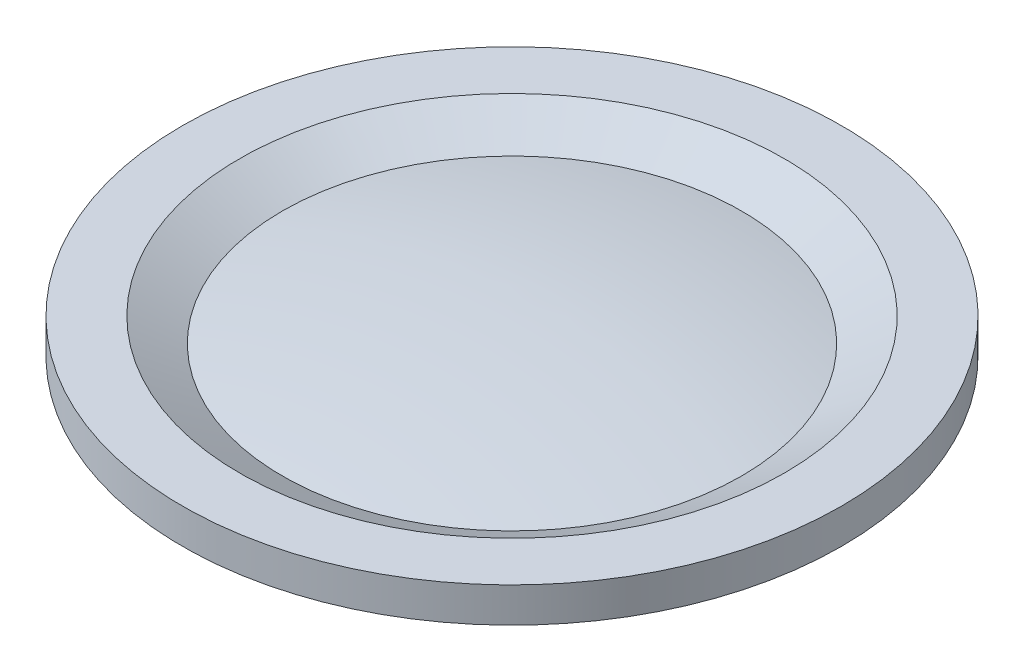
SolidWorks part; units mm, degrees
ref_plane "Front Plane" through (0, 0, 0) normal (0, 0, 1) x (1, 0, 0)
ref_plane "Top Plane" through (0, 0, 0) normal (0, 1, 0) x (1, 0, 0)
ref_plane "Right Plane" through (0, 0, 0) normal (1, 0, 0) x (0, 0, -1)
sketch "Sketch1" plane through (0, 0, 0) normal (0, 0, 1) x (1, 0, 0)
  line L0 (0, 0) -> (-8.1, 0)
  line L1 (-8.1, 0) -> (-8.1, 1.6)
  line L2 (-8.1, 1.6) -> (-14.4, 1.6)
  line L3 (-14.4, 1.6) -> (-15.75, 2.95)
  line L4 (-15.75, 2.95) -> (-17.95, 2.95)
  line L5 (-17.95, 2.95) -> (-17.95, 4.85)
  line L6 (-17.95, 4.85) -> (-14.8351, 4.85)
  line L7 (0, 4.85) -> (0, 0) construction
  line L8 (-14.8351, 4.85) -> (-12.5055, 3.5469)
  line L9 (-14.8351, 4.85) -> (0, 4.85) construction
  line L10 (0, 0) -> (0, 4.85)
  arc A0 (-12.5055, 3.5469) -> (0, 4.85) centre (0, -55.8061) cw
  dimension "D1" = 35.9
  dimension "D2" = 16.2
  dimension "D3" = 1.6
  dimension "D4" = 1.9
  dimension "D5" = 4.85
  dimension "D6" = 31.5
  dimension "D7" = 45
revolve "Revolve1" add sketch "Sketch1" angle 360 about L10
sketch "Sketch2" plane through (0, 1.6, 0) normal (0, -1, 0) x (1, 0, 0)
  line L0 (-7.275, -4.7712) -> (-7.275, -12.4272)
  line L1 (7.275, -4.7712) -> (7.275, -12.4272)
  line L2 (0, 0) -> (0, -14.4) construction
  arc A0 (-7.275, -4.7712) -> (7.275, -4.7712) centre (0, 0) ccw
  arc A1 (-7.275, -12.4272) -> (7.275, -12.4272) centre (0, 0) ccw
  circle A2 centre (0, 0) radius 14.4 construction
  dimension "D1" = 5.7
  dimension "D2" = 14.55
extrude "Boss-Extrude1" add sketch "Sketch2" along normal blind 1.44 separate body
